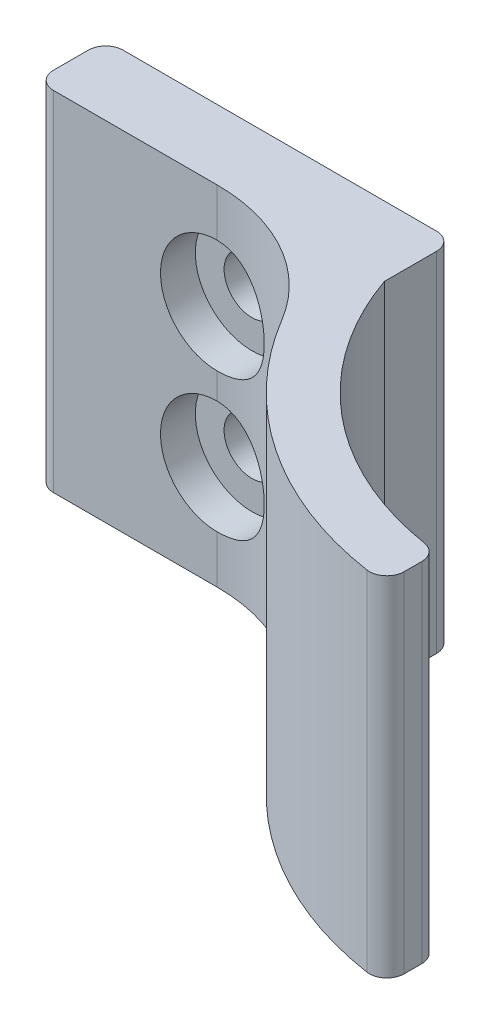
SolidWorks part; units mm, degrees
ref_plane "Front" through (0, 0, 0) normal (0, 0, 1) x (1, 0, 0)
ref_plane "Top" through (0, 0, 0) normal (0, 1, 0) x (1, 0, 0)
ref_plane "Right" through (0, 0, 0) normal (1, 0, 0) x (0, 0, -1)
sketch "Sketch1" plane through (0, 0, 0) normal (0, 1, 0) x (1, 0, 0)
  line L0 (15, -12.8456) -> (15, -13.8576)
  line L1 (-9.6022, 0) -> (-19, 0)
  line L2 (0, 0) -> (0, 3)
  line L3 (-1, 4) -> (-19, 4)
  line L4 (-20, 1) -> (-20, 3)
  arc A0 (0, 0) -> (14.1579, -11.8581) centre (17, 5.9161) ccw
  arc A1 (-1.0209, -4.8658) -> (13.85, -14.8463) centre (17, 5.9161) ccw
  arc A2 (-1.0209, -4.8658) -> (-9.6022, 0) centre (-9.6022, -10) ccw
  arc A3 (15, -13.8576) -> (13.85, -14.8463) centre (14, -13.8576) cw
  arc A4 (15, -12.8456) -> (14.1579, -11.8581) centre (14, -12.8456) ccw
  arc A5 (-19, 4) -> (-20, 3) centre (-19, 3) ccw
  arc A6 (-20, 1) -> (-19, 0) centre (-19, 1) ccw
  arc A7 (0, 3) -> (-1, 4) centre (-1, 3) ccw
  point P13 (15, -14.9885)
  point P16 (15, -11.9725)
  point P19 (-20, 4)
  point P22 (-20, 0)
  point P25 (0, 4)
  dimension "D1" = 18
  dimension "D2" = 0
  dimension "D6" = 3
  dimension "D7" = 10
  dimension "D8" = 1
  dimension "D9" = 1
  dimension "D10" = 17
  dimension "D3" = 15
  dimension "D4" = 4
  dimension "D5" = 20
extrude "Boss-Extrude1" add sketch "Sketch1" along normal blind 20
ref_plane "Plane1" through (0, 0, 2) normal (0, 0, 1) x (1, 0, 0)
hole_wizard "CBORE for M3 SHCS1" positions "Sketch2" profile "Sketch4" counterbore size "M3" standard "ANSI Metric"
sketch "Sketch2" plane through (0, 0, 0) normal (0, 0, 1) x (1, 0, 0)
  line L0 (-11.2777, 20) -> (-11.2777, 0) construction
  line L1 (-19, 20) -> (-11.2777, 20) construction
  line L2 (-19, 0) -> (-11.2777, 0) construction
  point P0 (-11.2777, 14)
  point P4 (-11.2777, 6)
  dimension "D1" = 6
  dimension "D2" = 6
sketch "Sketch4" plane through (-11.2777, 14, 0) normal (1, 0, 0) x (0, -1, 0)
  line L0 (0, 0) -> (0, 7.9614)
  line L1 (0, 7.9614) -> (1.6, 7)
  line L2 (1.6, 7) -> (1.6, 2)
  line L3 (1.6, 2) -> (3.25, 2)
  line L4 (3.25, 2) -> (3.25, 0)
  line L5 (3.25, 0) -> (0, 0)
  line L10 (0, 7.9614) -> (-1.6, 7) construction
  line L11 (0, -6.35) -> (0, 107.95) construction
  dimension "Hole Dia." = 3.2
  dimension "Hole Depth" = 7
  dimension "C'Bore Dia." = 6.5
  dimension "C'Bore Depth" = 2
  dimension "Drill Angle" = 118
hole_wizard "CBORE for M3 SHCS2" positions "Sketch6" profile "Sketch8" counterbore size "M3" standard "ANSI Metric" end condition through all
sketch "Sketch6" plane through (0, 0, 2) normal (0, 0, 1) x (1, 0, 0)
  line L0 (-9.6022, 20) -> (-9.6022, 0) construction
  line L1 (-19, 0) -> (-9.6022, 0) construction
  point P0 (-9.6022, 14)
  point P4 (-9.6022, 6)
  dimension "D1" = 8
  dimension "D2" = 6
sketch "Sketch8" plane through (-9.6022, 14, 2) normal (1, 0, 0) x (0, -1, 0)
  line L0 (0, 0) -> (0, 6)
  line L1 (0, 6) -> (1.6, 6)
  line L3 (1.6, 6) -> (1.6, 4)
  line L4 (1.6, 4) -> (3.25, 4)
  line L5 (3.25, 4) -> (3.25, 0)
  line L7 (3.25, 0) -> (0, 0)
  line L11 (0, -6.35) -> (0, 107.95) construction
  dimension "Thru Hole Dia." = 3.2
  dimension "Thru Hole Depth" = 6
  dimension "C'Bore Dia." = 6.5
  dimension "C'Bore Depth" = 4
